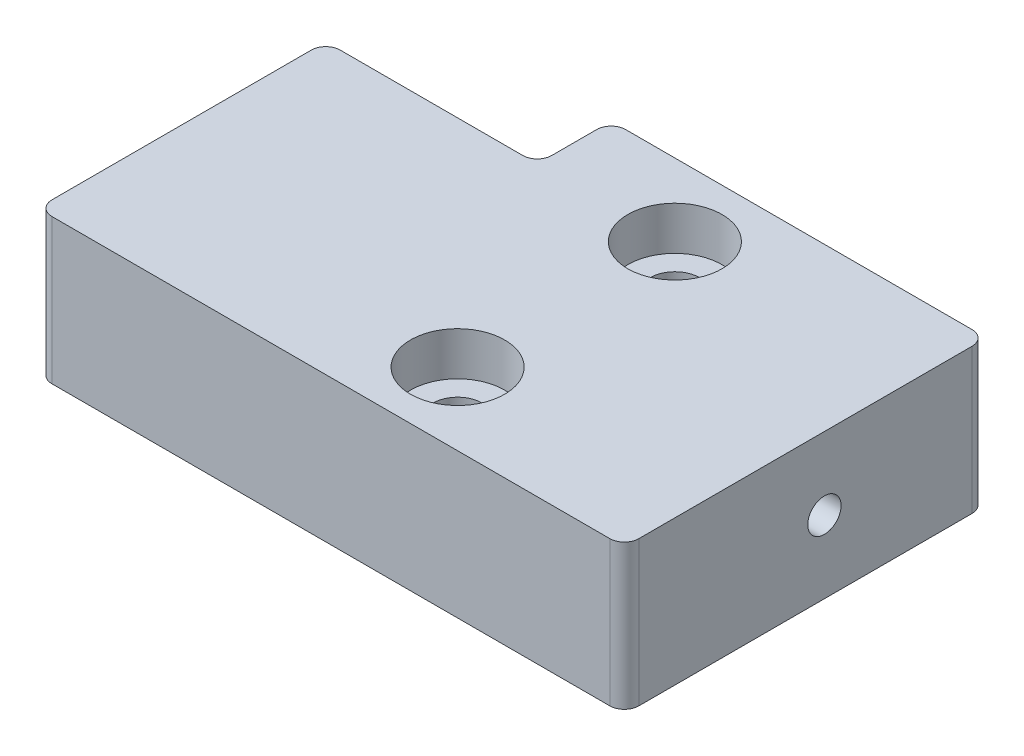
SolidWorks part; units mm, degrees
ref_plane "Front Plane" through (0, 0, 0) normal (0, 0, 1) x (1, 0, 0)
ref_plane "Top Plane" through (0, 0, 0) normal (0, 1, 0) x (1, 0, 0)
ref_plane "Right Plane" through (0, 0, 0) normal (1, 0, 0) x (0, 0, -1)
sketch "Sketch1" plane through (0, 0, 0) normal (0, 1, 0) x (1, 0, 0)
  line L0 (0, 0) -> (40.51, 0)
  line L1 (40.51, 0) -> (40.51, 25)
  line L2 (40.51, 25) -> (14.6, 25)
  line L3 (14.6, 25) -> (14.6, 19.9)
  line L4 (14.6, 19.9) -> (0, 19.9)
  line L5 (0, 19.9) -> (0, 0)
  dimension "D1" = 40.51
  dimension "D2" = 25
  dimension "D3" = 14.6
  dimension "D4" = 5.1
extrude "Boss-Extrude1" add sketch "Sketch1" along normal blind 10
fillet "Fillet1" radius 1 6 edges at (0, 5, -19.9) (14.6, 5, -19.9) (14.6, 5, -25) (40.51, 5, -25) (40.51, 5, 0) (0, 5, 0)
sketch "Sketch2" plane through (0, 10, 0) normal (0, 1, 0) x (1, 0, 0)
  line L0 (24, 25) -> (24, 0) construction
  line L1 (39.51, 25) -> (15.6, 25) construction
  line L2 (1, 0) -> (39.51, 0) construction
  line L3 (40.51, 1) -> (40.51, 24) construction
  line L4 (40.51, 12.5) -> (0, 12.5) construction
  line L5 (0, 18.9) -> (0, 1) construction
  point P12 (24, 20)
  point P13 (24, 5)
  point P14 (24, 12.5)
  dimension "D1" = 16.51
  dimension "D2" = 15
  dimension "D3" = 7.5
hole_wizard "CBORE for M3 SHCS1" positions "Sketch3" profile "Sketch4" counterbore size "M3" standard "ANSI Metric" end condition up to next
sketch "Sketch3" plane through (0, 10, 0) normal (0, 1, 0) x (1, 0, 0)
  point P0 (24, 20)
  point P3 (24, 5)
sketch "Sketch4" plane through (24, 10, -20) normal (1, 0, 0) x (0, 0, 1)
  line L0 (0, 0) -> (0, 10)
  line L1 (0, 10) -> (1.7, 10)
  line L3 (1.7, 10) -> (1.7, 3)
  line L4 (1.7, 3) -> (3.25, 3)
  line L5 (3.25, 3) -> (3.25, 0)
  line L7 (3.25, 0) -> (0, 0)
  line L11 (0, -6.35) -> (0, 107.95) construction
  dimension "Thru Hole Dia." = 3.4
  dimension "Thru Hole Depth" = 10
  dimension "C'Bore Dia." = 6.5
  dimension "C'Bore Depth" = 3
sketch "Sketch5" plane through (40.51, 0, 0) normal (1, 0, 0) x (0, 0, -1)
  circle A0 centre (13.81, 5) radius 1.15
  dimension "D1" = 2.3
extrude "Cut-Extrude1" cut sketch "Sketch5" against normal mid plane 5
